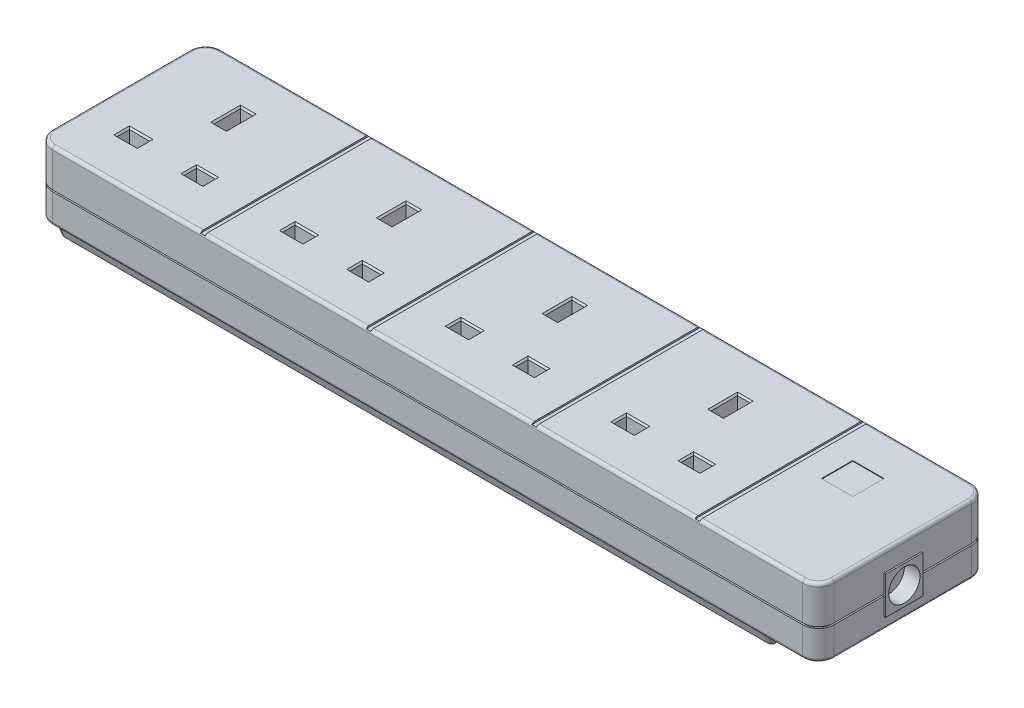
SolidWorks part; units mm, degrees
ref_plane "Front Plane" through (0, 0, 0) normal (0, 0, 1) x (1, 0, 0)
ref_plane "Top Plane" through (0, 0, 0) normal (0, 1, 0) x (1, 0, 0)
ref_plane "Right Plane" through (0, 0, 0) normal (1, 0, 0) x (0, 0, -1)
sketch "Sketch1" plane through (0, 0, 0) normal (0, 1, 0) x (1, 0, 0)
  line L1 (-120, 27) -> (120, 27)
  line L2 (-125, 22) -> (-125, -22)
  line L3 (-120, -27) -> (120, -27)
  line L4 (125, 22) -> (125, -22)
  line L5 (-125, 27) -> (125, -27) construction
  line L6 (-125, -27) -> (125, 27) construction
  arc A0 (120, -27) -> (125, -22) centre (120, -22) ccw
  arc A1 (120, 27) -> (125, 22) centre (120, 22) cw
  arc A2 (-120, 27) -> (-125, 22) centre (-120, 22) ccw
  arc A3 (-125, -22) -> (-120, -27) centre (-120, -22) ccw
  point P0 (0, 0)
  dimension "D3" = 5
  dimension "D1" = 250
  dimension "D2" = 54
extrude "Boss-Extrude1" add sketch "Sketch1" against normal blind 12
sketch "Sketch2" plane through (0, -12, 0) normal (0, -1, 0) x (1, 0, 0)
  line L0 (120, 26.5) -> (-120, 26.5)
  line L1 (-124.5, 22) -> (-124.5, -22)
  line L2 (-120, -26.5) -> (120, -26.5)
  line L3 (124.5, -22) -> (124.5, 22)
  line L4 (120, 27) -> (-120, 27)
  line L5 (-125, 22) -> (-125, -22)
  line L6 (-120, -27) -> (120, -27)
  line L7 (125, -22) -> (125, 22)
  line L8 (120, 27) -> (-120, 27) construction
  line L9 (-125, 22) -> (-125, -22) construction
  line L10 (-120, -27) -> (120, -27) construction
  line L11 (125, -22) -> (125, 22) construction
  arc A0 (-120, 26.5) -> (-124.5, 22) centre (-120, 22) ccw
  arc A1 (-124.5, -22) -> (-120, -26.5) centre (-120, -22) ccw
  arc A2 (120, -26.5) -> (124.5, -22) centre (120, -22) ccw
  arc A3 (124.5, 22) -> (120, 26.5) centre (120, 22) ccw
  arc A4 (125, 22) -> (120, 27) centre (120, 22) ccw
  arc A5 (-120, 27) -> (-125, 22) centre (-120, 22) ccw
  arc A6 (-125, -22) -> (-120, -27) centre (-120, -22) ccw
  arc A7 (120, -27) -> (125, -22) centre (120, -22) ccw
  arc A8 (125, 22) -> (120, 27) centre (120, 22) ccw construction
  arc A9 (-120, 27) -> (-125, 22) centre (-120, 22) ccw construction
  arc A10 (-125, -22) -> (-120, -27) centre (-120, -22) ccw construction
  arc A11 (120, -27) -> (125, -22) centre (120, -22) ccw construction
  dimension "D1" = 0
  dimension "D2" = 0.5
extrude "Boss-Extrude2" add sketch "Sketch2" along normal blind 0.5
sketch "Sketch3" plane through (0, -12.5, 0) normal (0, -1, 0) x (1, 0, 0)
  line L0 (125, 22) -> (125, -22) construction
  line L1 (-120, 27) -> (120, 27) construction
  line L2 (-125, -22) -> (-125, 22) construction
  line L3 (120, -27) -> (-120, -27) construction
  line L4 (125, 22) -> (125, -22)
  line L5 (-120, 27) -> (120, 27)
  line L6 (-125, -22) -> (-125, 22)
  line L7 (120, -27) -> (-120, -27)
  arc A0 (120, -27) -> (125, -22) centre (120, -22) ccw construction
  arc A1 (125, 22) -> (120, 27) centre (120, 22) ccw construction
  arc A2 (-120, 27) -> (-125, 22) centre (-120, 22) ccw construction
  arc A3 (-125, -22) -> (-120, -27) centre (-120, -22) ccw construction
  arc A4 (120, -27) -> (125, -22) centre (120, -22) ccw
  arc A5 (125, 22) -> (120, 27) centre (120, 22) ccw
  arc A6 (-120, 27) -> (-125, 22) centre (-120, 22) ccw
  arc A7 (-125, -22) -> (-120, -27) centre (-120, -22) ccw
extrude "Boss-Extrude3" add sketch "Sketch3" along normal blind 9.5
sketch "Sketch4" plane through (0, -22, 0) normal (0, -1, 0) x (1, 0, 0)
  line L4 (120, 27) -> (-120, 27) construction
  line L5 (-125, 22) -> (-125, -22) construction
  line L6 (-120, -27) -> (120, -27) construction
  line L7 (125, 22) -> (125, -22) construction
  line L12 (108, -22) -> (108, 22)
  line L13 (105, 25) -> (-120, 25)
  line L14 (-123, 22) -> (-123, -22)
  line L15 (-120, -25) -> (105, -25)
  arc A4 (-125, -22) -> (-120, -27) centre (-120, -22) ccw construction
  arc A5 (-120, 27) -> (-125, 22) centre (-120, 22) ccw construction
  arc A12 (105, -25) -> (108, -22) centre (105, -22) ccw
  arc A13 (108, 22) -> (105, 25) centre (105, 22) ccw
  arc A14 (-120, 25) -> (-123, 22) centre (-120, 22) ccw
  arc A15 (-123, -22) -> (-120, -25) centre (-120, -22) ccw
  dimension "D4" = 2
  dimension "D5" = 2
  dimension "D7" = 3
  dimension "D8" = 3
  dimension "D1" = 2
  dimension "D2" = 2
  dimension "D3" = 2
  dimension "D6" = 17
extrude "Boss-Extrude4" add sketch "Sketch4" along normal blind 5 draft 20
fillet "Fillet1" radius 1 16 edges at (-123.5355, 0, 25.5355) (-125, 0, 0) (-123.5355, 0, -25.5355) (0, 0, -27) (123.5355, 0, -25.5355) (125, 0, 0) (123.5355, 0, 25.5355) (123.5355, -22, 25.5355) (125, -22, 0) (123.5355, -22, -25.5355) (0, -22, -27) (-123.5355, -22, -25.5355) (-125, -22, 0) (-123.5355, -22, 25.5355) (0, 0, 27) (0, -22, 27)
sketch "Sketch5" plane through (0, 0, 0) normal (0, 1, 0) x (1, 0, 0)
  line L0 (125, 22) -> (125, -22) construction
  line L1 (-120, 27) -> (120, 27) construction
  line L2 (-125, -22) -> (-125, 22) construction
  line L3 (120, -27) -> (-120, -27) construction
  line L4 (125, 22) -> (125, -22) construction
  line L5 (-120, 27) -> (120, 27) construction
  line L6 (-125, -22) -> (-125, 22) construction
  line L7 (120, -27) -> (-120, -27) construction
  line L8 (87, 27) -> (87, -27) construction
  line L9 (87, -27) -> (-125, 27) construction
  line L10 (-125, 27) -> (-19, -27) construction
  line L11 (-19, -27) -> (-19, 27) construction
  line L12 (-19, 27) -> (87, -27) construction
  line L13 (34, 27) -> (34, -27) construction
  line L14 (34, -27) -> (-72, 27) construction
  line L15 (-72, 27) -> (-72, -27) construction
  line L17 (-71.25, -27) -> (-72.75, -27)
  line L18 (-71.25, -27) -> (-71.25, 27)
  line L19 (-71.25, 27) -> (-72.75, 27)
  line L20 (-72.75, -27) -> (-72.75, 27)
  line L21 (-71.25, -27) -> (-72.75, 27) construction
  line L22 (-71.25, 27) -> (-72.75, -27) construction
  line L23 (-18.25, -27) -> (-19.75, -27)
  line L24 (-18.25, -27) -> (-18.25, 27)
  line L25 (-18.25, 27) -> (-19.75, 27)
  line L26 (-19.75, -27) -> (-19.75, 27)
  line L27 (-18.25, -27) -> (-19.75, 27) construction
  line L28 (-18.25, 27) -> (-19.75, -27) construction
  line L29 (34.75, -27) -> (33.25, -27)
  line L30 (34.75, -27) -> (34.75, 27)
  line L31 (34.75, 27) -> (33.25, 27)
  line L32 (33.25, -27) -> (33.25, 27)
  line L33 (34.75, -27) -> (33.25, 27) construction
  line L34 (34.75, 27) -> (33.25, -27) construction
  line L35 (87, -27) -> (85.5, -27)
  line L36 (87, -27) -> (87, 27)
  line L37 (87, 27) -> (85.5, 27)
  line L38 (85.5, -27) -> (85.5, 27)
  arc A0 (120, -27) -> (125, -22) centre (120, -22) ccw construction
  arc A1 (125, 22) -> (120, 27) centre (120, 22) ccw construction
  arc A2 (-120, 27) -> (-125, 22) centre (-120, 22) ccw construction
  arc A3 (-125, -22) -> (-120, -27) centre (-120, -22) ccw construction
  arc A4 (120, -27) -> (125, -22) centre (120, -22) ccw construction
  arc A5 (125, 22) -> (120, 27) centre (120, 22) ccw construction
  arc A6 (-120, 27) -> (-125, 22) centre (-120, 22) ccw construction
  arc A7 (-125, -22) -> (-120, -27) centre (-120, -22) ccw construction
  point P19 (-19, 0)
  point P23 (-72, 0)
  point P24 (-72, 0)
  point P32 (34, 0)
  dimension "D1" = 38
  dimension "D2" = 1.5
  dimension "D3" = 1.5
  dimension "D4" = 1.5
  dimension "D5" = 1.5
extrude "Cut-Extrude1" cut sketch "Sketch5" against normal blind 0.5
sketch "Sketch6" plane through (0, 0, 0) normal (0, 1, 0) x (1, 0, 0)
  line L0 (125, 22) -> (125, -22) construction
  line L1 (95, 14) -> (105, 14)
  line L2 (95, 14) -> (95, 4)
  line L3 (95, 4) -> (105, 4)
  line L4 (105, 14) -> (105, 4)
  line L5 (-120, 27) -> (120, 27) construction
  dimension "D1" = 10
  dimension "D2" = 10
  dimension "D3" = 20
  dimension "D4" = 13
extrude "Cut-Extrude2" cut sketch "Sketch6" against normal blind 2
sketch "Sketch7" plane through (0, -2, 0) normal (0, 1, 0) x (1, 0, 0)
  line L0 (95, 14) -> (95, 4) construction
  line L1 (96, 13) -> (104, 13)
  line L2 (96, 13) -> (96, 5)
  line L3 (96, 5) -> (104, 5)
  line L4 (104, 13) -> (104, 5)
  line L5 (105, 14) -> (95, 14) construction
  line L6 (105, 4) -> (105, 14) construction
  line L8 (95, 4) -> (105, 4) construction
  dimension "D1" = 1
  dimension "D2" = 1
  dimension "D3" = 1
  dimension "D4" = 1
extrude "Cut-Extrude3" cut sketch "Sketch7" against normal blind 10
sketch "Sketch8" plane through (0, -2, 0) normal (0, 1, 0) x (1, 0, 0)
  line L0 (105, 14) -> (95, 14) construction
  line L1 (95.1, 13.9) -> (104.9, 13.9)
  line L2 (95.1, 13.9) -> (95.1, 4.1)
  line L3 (95.1, 4.1) -> (104.9, 4.1)
  line L4 (104.9, 13.9) -> (104.9, 4.1)
  line L5 (95, 14) -> (95, 4) construction
  line L6 (105, 4) -> (105, 14) construction
  line L7 (95, 4) -> (105, 4) construction
  dimension "D1" = 0.1
  dimension "D2" = 0.1
  dimension "D3" = 0.1
  dimension "D4" = 0.1
extrude "Boss-Extrude5" add sketch "Sketch8" along normal blind 1.9 separate body
sketch "Sketch9" plane through (0, 0, 0) normal (0, 1, 0) x (1, 0, 0)
  line L0 (60.125, 26) -> (60.125, -26) construction
  line L1 (58.125, 14) -> (62.125, 14)
  line L2 (58.125, 14) -> (58.125, 5.5)
  line L3 (58.125, 5.5) -> (62.125, 5.5)
  line L4 (62.125, 14) -> (62.125, 5.5)
  line L5 (46.125, -9.5) -> (52.625, -9.5)
  line L6 (46.125, -9.5) -> (46.125, -13.5)
  line L7 (46.125, -13.5) -> (52.625, -13.5)
  line L8 (52.625, -9.5) -> (52.625, -13.5)
  line L9 (67.625, -9.5) -> (73.625, -9.5)
  line L10 (67.625, -9.5) -> (67.625, -13.5)
  line L11 (67.625, -13.5) -> (73.625, -13.5)
  line L12 (73.625, -9.5) -> (73.625, -13.5)
  line L13 (85.5, 26) -> (34.75, 26) construction
  line L14 (34.75, -26) -> (85.5, -26) construction
  line L15 (-120, 27) -> (120, 27) construction
  line L16 (52.625, -9.5) -> (67.625, -9.5) construction
  point P20 (60.125, 14)
  point P21 (60.125, -9.5)
  dimension "D1" = 6.5
  dimension "D2" = 8.5
  dimension "D3" = 6
  dimension "D4" = 15
  dimension "D5" = 15
  dimension "D6" = 13
  dimension "D7" = 4
  dimension "D8" = 4
  dimension "D9" = 4
extrude "Cut-Extrude4" cut sketch "Sketch9" against normal blind 10
chamfer "Chamfer1" distance 0.5 angle 45 12 edges at (70.625, 0, 13.5) (73.625, 0, 11.5) (70.625, 0, 9.5) (67.625, 0, 11.5) (49.375, 0, 13.5) (52.625, 0, 11.5) (46.125, 0, 11.5) (49.375, 0, 9.5) (62.125, 0, -9.75) (60.125, 0, -5.5) (58.125, 0, -9.75) (60.125, 0, -14)
pattern_linear "LPattern1" count 4 spacing 53 along (-1, 0, 0) of "Cut-Extrude4", "Chamfer1"
sketch "Sketch10" plane through (125, 0, 0) normal (1, 0, 0) x (0, 0, -1)
  line L0 (0, 0) -> (0, -22) construction
  line L1 (22, -22) -> (-22, -22) construction
  line L2 (-22, 0) -> (22, 0) construction
  line L3 (-6, -18.25) -> (6, -18.25)
  line L4 (-6, -18.25) -> (-6, -6.25)
  line L5 (-6, -6.25) -> (6, -6.25)
  line L6 (6, -18.25) -> (6, -6.25)
  line L7 (-6, -18.25) -> (6, -6.25) construction
  line L8 (-6, -6.25) -> (6, -18.25) construction
  circle A0 centre (0, -12.25) radius 5
  dimension "D3" = 10
  dimension "D4" = 12.25
  dimension "D1" = 12
  dimension "D2" = 12
extrude "Boss-Extrude6" add sketch "Sketch10" along normal blind 0.5 and the other way blind 5
sketch "Sketch11" plane through (125.5, 0, 0) normal (1, 0, 0) x (0, 0, -1)
  circle A0 centre (0, -12.25) radius 5 construction
  circle A1 centre (0, -12.25) radius 5
extrude "Cut-Extrude5" cut sketch "Sketch11" against normal blind 5
sketch "Sketch12" plane through (0, -27, 0) normal (0, -1, 0) x (1, 0, 0)
  line L0 (-118.8365, -2) -> (156.7174, -2) construction
  line L1 (-80, -9.5693) -> (-80, -9) construction
  line L2 (-77.5, -5.4369) -> (-77.5, -9)
  line L3 (-82.5, -5.4369) -> (-82.5, -9)
  line L4 (74, -9) -> (74, -6.0953) construction
  line L5 (71.5, -9) -> (71.5, -5.4369)
  line L6 (76.5, -9) -> (76.5, -5.4369)
  line L7 (125, 22) -> (125, -22) construction
  line L8 (120, -27) -> (-120, -27) construction
  arc A0 (-77.5, -5.4369) -> (-82.5, -5.4369) centre (-80, -2) ccw
  arc A1 (76.5, -5.4369) -> (71.5, -5.4369) centre (74, -2) ccw
  arc A3 (-82.5, -9) -> (-77.5, -9) centre (-80, -9) ccw
  arc A4 (71.5, -9) -> (76.5, -9) centre (74, -9) ccw
  point P8 (-80, -6.25)
  point P14 (74, -6.25)
  dimension "D3" = 4.25
  dimension "D4" = 4.25
  dimension "D1" = 51
  dimension "D2" = 154
  dimension "D5" = 5
  dimension "D6" = 5
  dimension "D7" = 7
  dimension "D8" = 25
extrude "Cut-Extrude6" cut sketch "Sketch12" against normal blind 5
sketch "Sketch13" plane through (0, -22, 0) normal (0, -1, 0) x (1, 0, 0)
  line L0 (-80, -2) -> (-80, -9) construction
  line L1 (-75.75, -2) -> (-75.75, -9)
  line L2 (-84.25, -2) -> (-84.25, -9)
  line L3 (74, -2) -> (74, -9) construction
  line L4 (78.25, -2) -> (78.25, -9)
  line L5 (69.75, -2) -> (69.75, -9)
  arc A0 (-75.75, -2) -> (-84.25, -2) centre (-80, -2) ccw
  arc A1 (-84.25, -9) -> (-75.75, -9) centre (-80, -9) ccw
  arc A2 (78.25, -2) -> (69.75, -2) centre (74, -2) ccw
  arc A3 (69.75, -9) -> (78.25, -9) centre (74, -9) ccw
  arc A4 (76.5, -5.4369) -> (71.5, -5.4369) centre (74, -2) ccw construction
  arc A5 (-77.5, -5.4369) -> (-82.5, -5.4369) centre (-80, -2) ccw construction
  point P4 (-80, -5.5)
  point P9 (74, -5.5)
extrude "Cut-Extrude7" cut sketch "Sketch13" along normal blind 3.5
